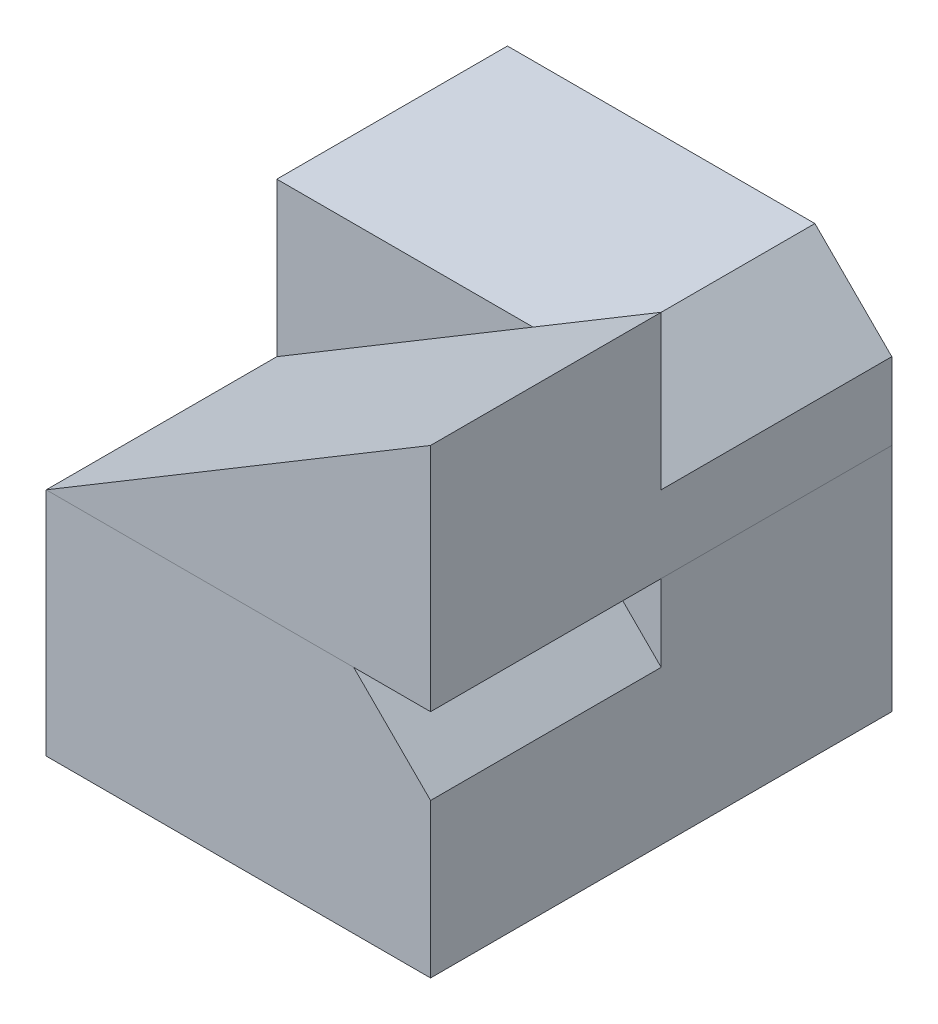
SolidWorks part; units mm, degrees
ref_plane "Front Plane" through (0, 0, 0) normal (0, 0, 1) x (1, 0, 0)
ref_plane "Top Plane" through (0, 0, 0) normal (0, 1, 0) x (1, 0, 0)
ref_plane "Right Plane" through (0, 0, 0) normal (1, 0, 0) x (0, 0, -1)
sketch "Sketch1" plane through (0, 0, 0) normal (0, 0, 1) x (1, 0, 0)
  line L0 (-25, 0) -> (0, 0)
  line L1 (0, 0) -> (0, 15)
  line L2 (0, 15) -> (-25, 0)
  dimension "D1" = 25
  dimension "D2" = 15
extrude "Boss-Extrude1" add sketch "Sketch1" along normal blind 15
sketch "Sketch2" plane through (0, 0, 15) normal (0, 0, 1) x (1, 0, 0)
  line L0 (-25, 0) -> (-25, 15)
  line L1 (-25, 15) -> (-5, 15)
  line L2 (-5, 15) -> (0, 10)
  line L3 (0, 10) -> (0, 0)
  line L4 (0, 0) -> (-25, 0)
  dimension "D1" = 20
  dimension "D2" = 10
  dimension "D3" = 25
  dimension "D4" = 15
extrude "Boss-Extrude2" add sketch "Sketch2" along normal blind 15
sketch "Sketch3" plane through (0, 0, 15) normal (0, 0, 1) x (1, 0, 0)
  line L0 (-25, 15) -> (0, 15)
  line L1 (0, 15) -> (0, 30)
  line L2 (0, 30) -> (-25, 15)
  dimension "D1" = 25
  dimension "15" = 15
extrude "Boss-Extrude4" add sketch "Sketch3" along normal blind 15 separate body
sketch "Sketch5" plane through (0, 0, 15) normal (0, 0, -1) x (-1, 0, 0)
  line L0 (25, 15) -> (25, 25)
  line L1 (25, 25) -> (5, 25)
  line L3 (5, 25) -> (0, 20)
  line L4 (0, 20) -> (0, 15)
  line L5 (0, 15) -> (25, 15)
  line L6 (0, 0) -> (0, 15) construction
  line L7 (0, 15) -> (25, 0) construction
  line L8 (0, 15) -> (0, 30) construction
  dimension "D1" = 10
  dimension "D2" = 20
  dimension "D3" = 5
extrude "Boss-Extrude5" add sketch "Sketch5" along normal blind 15
